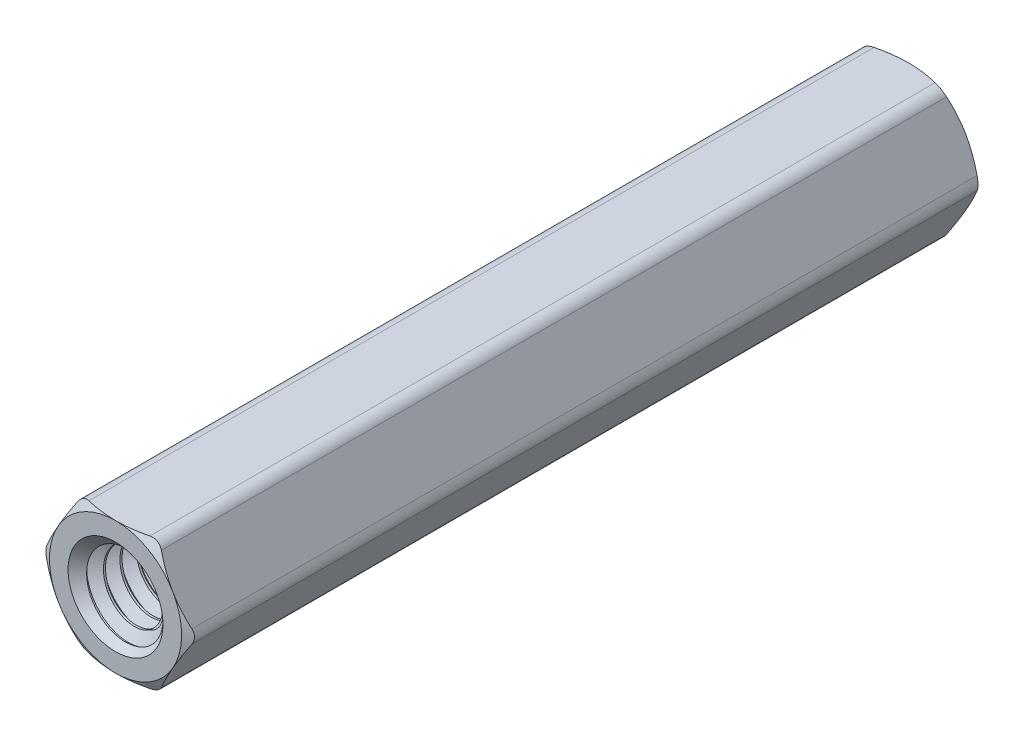
SolidWorks part; units mm, degrees
ref_plane "Front Plane" through (0, 0, 0) normal (0, 0, 1) x (1, 0, 0)
ref_plane "Top Plane" through (0, 0, 0) normal (0, 1, 0) x (1, 0, 0)
ref_plane "Right Plane" through (0, 0, 0) normal (1, 0, 0) x (0, 0, -1)
sketch "Sketch1" plane through (0, 0, 0) normal (0, 0, 1) x (1, 0, 0)
  line L0 (0, 0) -> (3.6662, 0) construction
  line L1 (1.8331, -3.175) -> (3.6662, 0)
  line L2 (3.6662, 0) -> (1.8331, 3.175)
  line L3 (1.8331, 3.175) -> (-1.8331, 3.175)
  line L4 (-1.8331, 3.175) -> (-3.6662, 0)
  line L5 (-3.6662, 0) -> (-1.8331, -3.175)
  line L6 (-1.8331, -3.175) -> (1.8331, -3.175)
  circle A0 centre (0, 0) radius 3.175 construction
  point P10 (0, -3.175)
  dimension "Hex Size" = 6.35
sketch "Sketch2" plane through (0, 0, 0) normal (1, 0, 0) x (0, 0, -1)
  line L0 (-9.525, 0) -> (-19.05, 0) construction
  line L3 (-9.525, 2.0828) -> (-9.525, -2.0828) construction
  line L4 (-19.7941, 2.1687) -> (-19.3973, 1.4813) construction
  line L5 (-19.3973, 1.4813) -> (-19.0004, 2.1687) construction
  line L6 (-19.0004, 2.1687) -> (-19.7941, 2.1687) construction
  line L7 (-19.7445, 2.0828) -> (-19.05, 2.0828) construction
  line L8 (-19.4469, 1.5672) -> (-19.3477, 1.5672) construction
  line L9 (-19.3973, 1.5672) -> (-19.3973, 1.4813) construction
  line L10 (-19.3973, 2.0828) -> (-19.3973, 2.1687) construction
  line L11 (19.05, 3.175) -> (-19.05, 3.175) construction
  point P6 (0, 3.175)
  point P9 (-9.525, 0)
  dimension "Minimum Thread Length" = 9.525
  dimension "Thread Size" = 4.1656
  dimension "Thread Pitch" = 0.7937
  dimension "Thread Pitch (B)/8" = 0.0992
  dimension "Length" = 38.1
sketch "Sketch3" plane through (0, 0, 0) normal (1, 0, 0) x (0, 0, -1)
  line L1 (-9.525, 2.0828) -> (-9.525, 0)
  line L2 (19.05, 3.175) -> (19.05, 2.0828)
  line L6 (19.05, 3.175) -> (19.05, 2.0828)
  line L8 (19.05, 2.0828) -> (9.525, 2.0828)
  line L9 (-18.8516, 2.0828) -> (-19.05, 2.2812)
  line L10 (0, 3.175) -> (19.05, 3.175)
  line L11 (-19.05, 2.2812) -> (-19.05, 3.175)
  line L12 (-19.05, 3.175) -> (0, 3.175)
  line L13 (-9.525, 0) -> (9.525, 0)
  line L14 (9.525, 0) -> (9.525, 2.0828)
  line L16 (-9.525, 2.0828) -> (-18.8516, 2.0828)
  point P5 (-19.05, -3.175)
  dimension "D1" = 45
  dimension "D3" = 0.1984
revolve "Revolve1" add sketch "Sketch3" angle 360 about L0
sketch "Sketch4" plane through (0, 0, 0) normal (0, 0, 1) x (1, 0, 0)
  line L0 (0, 3.175) -> (0, 2.0828) construction
  line L1 (-1.8331, 3.175) -> (-3.6662, 0)
  line L2 (-3.6662, 0) -> (-1.8331, -3.175)
  line L3 (-1.8331, -3.175) -> (1.8331, -3.175)
  line L4 (1.8331, -3.175) -> (3.6662, 0)
  line L5 (3.6662, 0) -> (1.8331, 3.175)
  line L6 (1.8331, 3.175) -> (-1.8331, 3.175)
  line L7 (1.8331, -3.175) -> (3.6662, 0) construction
  circle A0 centre (0, 0) radius 3.175 construction
  circle A1 centre (0, 0) radius 2.6289
  circle A2 centre (0, 0) radius 3.175 construction
  point P16 (0, 2.6289)
extrude "Boss-Extrude1" add sketch "Sketch4" against normal mid plane 38.1
sketch "Sketch5" plane through (0, 0, 19.05) normal (0, 0, 1) x (1, 0, 0)
  line L0 (0, 2.0828) -> (0, -2.0828) construction
  line L1 (0, 2.0828) -> (0, -2.0828) construction
  circle A0 centre (0, 0) radius 3.175
  circle A1 centre (0, 0) radius 3.175 construction
  point P11 (0, -2.0828)
extrude "Cut-Extrude1" cut sketch "Sketch5" against normal through all draft 60 flip side to cut
sketch "Sketch6" plane through (0, 0, -19.05) normal (0, 0, -1) x (-1, 0, 0)
  circle A0 centre (0, 0) radius 3.175
  circle A1 centre (0, 0) radius 3.175 construction
extrude "Cut-Extrude2" cut sketch "Sketch6" against normal through all draft 60 flip side to cut
fillet "Fillet1" radius 0.635 6 edges at (1.8331, 3.175, 0) (-3.6662, 0, 0) (-1.8331, -3.175, 0) (1.8331, -3.175, 0) (3.6662, 0, 0) (-1.8331, 3.175, 0)
sketch "Drawing 1" plane through (0, 0, 0) normal (1, 0, 0) x (0, 0, -1)
  line L0 (-9.525, -2.0828) -> (-19.05, -2.0828) construction
  line L1 (-9.525, 2.0828) -> (-19.05, 2.0828) construction
  line L2 (19.05, 2.0828) -> (9.525, 2.0828) construction
  line L3 (-9.525, 0) -> (-19.05, 0) construction
  line L4 (9.525, 2.0828) -> (9.525, -2.0828) construction
  line L5 (9.525, -2.0828) -> (19.05, -2.0828) construction
  line L6 (-9.525, 2.0828) -> (-9.525, -2.0828) construction
split "Split1" trim tools "Front Plane" bodies to split 107 resulting bodies 120
sketch "Sketch7" plane through (0, 0, 9.525) normal (0, 0, -1) x (-1, 0, 0)
  circle A0 centre (0, 0) radius 2.2812
extrude "Boss-Extrude2" add sketch "Sketch7" along normal up to surface (9.525 mm away)
sketch "Sketch8" plane through (0, 0, 0) normal (1, 0, 0) x (0, 0, -1)
  line L0 (-9.525, 0) -> (-19.05, 0) construction
  line L1 (-9.525, 2.0828) -> (-19.05, 2.0828)
  line L2 (-9.525, 2.0828) -> (-9.525, 0)
  line L3 (-9.525, 0) -> (-19.05, 0)
  line L4 (-19.05, 2.0828) -> (-19.05, 0)
revolve "Revolve2" add sketch "Sketch8" angle 360 about L0
sketch "Sketch9" plane through (0, 0, 19.05) normal (0, 0, 1) x (1, 0, 0)
  circle A0 centre (0, 0) radius 2.0828
  circle A1 centre (0, 0) radius 2.0828 construction
sketch "Sketch10" plane through (0, 0, 0) normal (1, 0, 0) x (0, 0, -1)
  line L0 (-19.4469, 1.5672) -> (-19.3477, 1.5672)
  line L1 (-19.3477, 1.5672) -> (-19.0252, 2.1258)
  line L2 (-19.3973, 1.4813) -> (-19.0004, 2.1687) construction
  line L3 (-19.0252, 2.1258) -> (-19.7693, 2.1258)
  line L4 (-19.7941, 2.1687) -> (-19.3973, 1.4813) construction
  line L5 (-19.7693, 2.1258) -> (-19.4469, 1.5672)
  line L6 (-19.3973, 2.0828) -> (-19.3973, 2.1687) construction
  point P12 (-19.3973, 2.1258)
curve "Helix/Spiral1" pitch 0.7937 height 10.3187 turns 13
sweep "Cut-Sweep1" cut profiles "Sketch10" path "Helix/Spiral1"
combine bodies "Combine1" operation type subtract main body 113 bodies to subtract 114
ref_plane "Plane1" through (0, 0, 18.8516) normal (0, 0, 1) x (1, 0, 0)
sketch "Sketch11" plane through (0, 0, 19.05) normal (0, 0, 1) x (1, 0, 0)
  circle A0 centre (0, 0) radius 2.2812
extrude "Cut-Extrude3" cut sketch "Sketch11" against normal through all draft 45
pattern_circular "CirPattern1" count 2 over 360 about axis through (0, 0, 0) along (1, 0, 0) of bodies 116 118
combine bodies "Combine2" bodies to combine 116 121
equation "\"Thread Pitch (B)/8@Sketch2\" = \"Thread Pitch@Sketch2\" / 8"
equation "\"D1@Fillet1\" = \"Hex Size@Sketch1\" * .1"
equation "\"D3@Helix/Spiral1\" = \"Minimum Thread Length@Sketch2\" + \"Thread Pitch@Sketch2\""
equation "\"D4@Helix/Spiral1\" = \"Thread Pitch@Sketch2\""
equation "\"D1@Boss-Extrude1\" = \"Length@Sketch2\""
equation "\"D3@Sketch3\"=\"Thread Pitch@Sketch2\"*.25"
